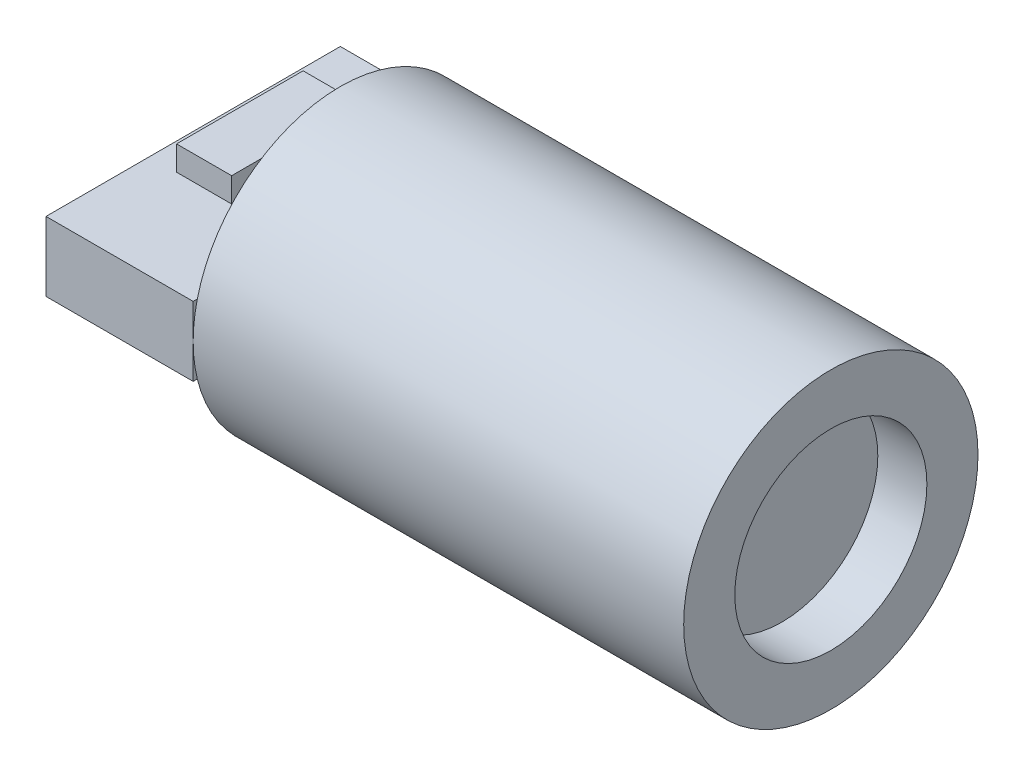
SolidWorks part; units mm, degrees
ref_plane "Front Plane" through (0, 0, 0) normal (0, 0, 1) x (1, 0, 0)
ref_plane "Top Plane" through (0, 0, 0) normal (0, 1, 0) x (1, 0, 0)
ref_plane "Right Plane" through (0, 0, 0) normal (1, 0, 0) x (0, 0, -1)
sketch "Sketch1" plane through (0, 0, 0) normal (1, 0, 0) x (0, 0, -1)
  circle A0 centre (0, 0) radius 3
  dimension "D1" = 6
extrude "Boss-Extrude1" add sketch "Sketch1" along normal blind 10
sketch "Sketch2" plane through (10, 0, 0) normal (1, 0, 0) x (0, 0, -1)
  circle A0 centre (0, 0) radius 1.9579
extrude "Cut-Extrude1" cut sketch "Sketch2" against normal blind 1
sketch "Sketch3" plane through (0, 0, 0) normal (-1, 0, 0) x (0, 0, 1)
  line L1 (-3, 0.7067) -> (3, 0.7067)
  line L2 (-3, 0.7067) -> (-3, -0.7067)
  line L3 (-3, -0.7067) -> (3, -0.7067)
  line L4 (3, 0.7067) -> (3, -0.7067)
  line L5 (-3, 0.7067) -> (3, -0.7067) construction
  line L6 (-3, -0.7067) -> (3, 0.7067) construction
  point P0 (0, 0)
extrude "Boss-Extrude2" add sketch "Sketch3" along normal blind 3
sketch "Sketch4" plane through (0, 0.7067, 0) normal (0, 1, 0) x (1, 0, 0)
  line L1 (-2.4496, 1.6913) -> (-1.3266, 1.6913)
  line L2 (-2.4496, 1.6913) -> (-2.4496, -0.8891)
  line L3 (-2.4496, -0.8891) -> (-1.3266, -0.8891)
  line L4 (-1.3266, 1.6913) -> (-1.3266, -0.8891)
extrude "Boss-Extrude3" add sketch "Sketch4" along normal blind 0.5
